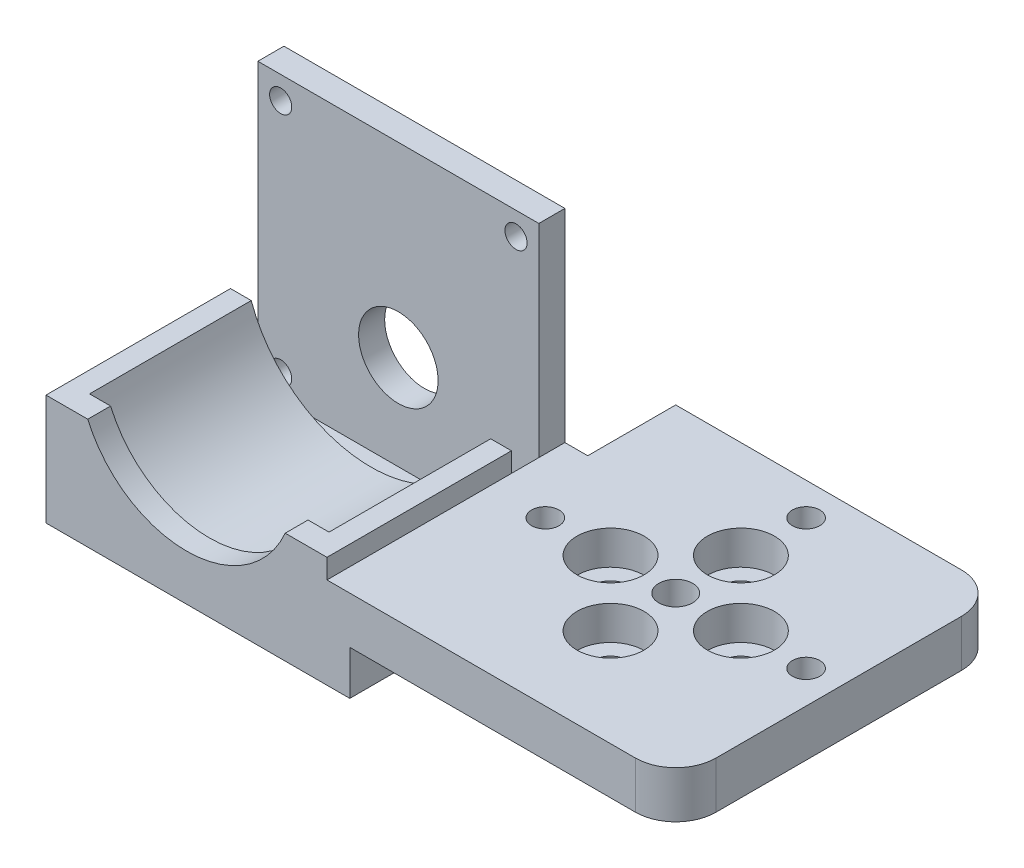
SolidWorks part; units mm, degrees
ref_plane "정면" through (0, 0, 0) normal (0, 0, 1) x (1, 0, 0)
ref_plane "윗면" through (0, 0, 0) normal (0, 1, 0) x (1, 0, 0)
ref_plane "우측면" through (0, 0, 0) normal (1, 0, 0) x (0, 0, -1)
sketch "스케치2" plane through (0, 0, 0) normal (0, 1, 0) x (1, 0, 0)
  line L1 (-25, 25) -> (25, 25)
  line L2 (-25, 25) -> (-25, -25)
  line L3 (-25, -25) -> (25, -25)
  line L4 (25, 25) -> (25, -25)
  line L5 (-25, 25) -> (25, -25) construction
  line L6 (-25, -25) -> (25, 25) construction
  circle A0 centre (0, 0) radius 2.6
  circle A1 centre (10, 0) radius 2.6
  circle A2 centre (0, -10) radius 2.6
  circle A3 centre (-10, 0) radius 2.6
  circle A4 centre (0, 10) radius 2.6
  point P4 (0, 0)
  point P19 (0, 0)
  dimension "D3" = 5.2
  dimension "D1" = 50
  dimension "D2" = 50
  dimension "D4" = 10
  dimension "D5" = 4
extrude "보스-돌출1" add sketch "스케치2" along normal blind 2
sketch "스케치3" plane through (0, 2, 0) normal (0, 1, 0) x (1, 0, 0)
  line L0 (25, -25) -> (25, 25) construction
  line L1 (-25, 25) -> (25, 25)
  line L2 (-25, 25) -> (-25, -25)
  line L3 (-25, -25) -> (25, -25)
  line L4 (25, 25) -> (25, -25)
  line L5 (-25, 25) -> (25, -25) construction
  line L6 (-25, -25) -> (25, 25) construction
  circle A0 centre (0, 0) radius 5.15 construction
  circle A1 centre (10, 0) radius 5.15
  circle A2 centre (10, 0) radius 2.6 construction
  circle A3 centre (0, -10) radius 5.15
  circle A4 centre (-10, 0) radius 5.15
  circle A5 centre (0, 10) radius 5.15
  circle A6 centre (-10, 0) radius 2.6 construction
  point P15 (0, 0)
  point P23 (0, 0)
  dimension "D1" = 10.3
  dimension "D2" = 4
extrude "보스-돌출2" add sketch "스케치3" along normal blind 5.2
sketch "스케치4" plane through (0, 7.2, 0) normal (0, 1, 0) x (1, 0, 0)
  line L0 (-25, -25) -> (25, -25) construction
  line L1 (-10, 10) -> (10, 10) construction
  line L2 (-10, 10) -> (-10, -25) construction
  line L3 (-10, -25) -> (10, -25) construction
  line L4 (10, 10) -> (10, -25) construction
  line L5 (-10, 10) -> (10, -25) construction
  line L6 (-10, -25) -> (10, 10) construction
  line L7 (0, 0) -> (20, 0) construction
  line L8 (0, 0) -> (0, 20) construction
  circle A2 centre (20, 0) radius 2.1
  circle A3 centre (0, 20) radius 2.1
  circle A4 centre (-20, 0) radius 2.1
  point P4 (0, -7.5)
  point P8 (0, -25)
  dimension "D4" = 4.2
  dimension "D1" = 20
  dimension "D2" = 10
  dimension "D3" = 20
  dimension "D6" = 90
  dimension "D5" = 3
extrude "컷-돌출1" cut sketch "스케치4" against normal blind 10
sketch "스케치6" plane through (0, 0, 0) normal (0, -1, 0) x (1, 0, 0)
  line L13 (-25, -25) -> (-25, 25) construction
  line L14 (-16.45, -2.0496) -> (-16.45, 2.0496)
  line L15 (-16.45, 2.0496) -> (-20, 4.0992)
  line L16 (-20, 4.0992) -> (-23.55, 2.0496)
  line L17 (-23.55, 2.0496) -> (-23.55, -2.0496)
  line L18 (-23.55, -2.0496) -> (-20, -4.0992)
  line L19 (-20, -4.0992) -> (-16.45, -2.0496)
  line L20 (2.0496, -16.45) -> (-2.0496, -16.45)
  line L21 (-2.0496, -16.45) -> (-4.0992, -20)
  line L22 (-4.0992, -20) -> (-2.0496, -23.55)
  line L23 (-2.0496, -23.55) -> (2.0496, -23.55)
  line L24 (2.0496, -23.55) -> (4.0992, -20)
  line L25 (4.0992, -20) -> (2.0496, -16.45)
  line L26 (16.45, 2.0496) -> (16.45, -2.0496)
  line L27 (16.45, -2.0496) -> (20, -4.0992)
  line L28 (20, -4.0992) -> (23.55, -2.0496)
  line L29 (23.55, -2.0496) -> (23.55, 2.0496)
  line L30 (23.55, 2.0496) -> (20, 4.0992)
  line L31 (20, 4.0992) -> (16.45, 2.0496)
  line L32 (0, 0) -> (-16.45, 2.0496) construction
  line L33 (0, 0) -> (-2.0496, -16.45) construction
  circle A0 centre (-20, 0) radius 3.55 construction
  circle A2 centre (0, -20) radius 3.55 construction
  circle A3 centre (20, 0) radius 3.55 construction
  dimension "D1" = 7.1
  dimension "D3" = 90
  dimension "D2" = 3
extrude "컷-돌출2" cut sketch "스케치6" against normal blind 3.5
fillet "필렛1" radius 6.17 1 edges at (25, 3.6, -25)
fillet "필렛2" radius 6.17 1 edges at (25, 3.6, 25)
ref_plane "평면1" through (0, 0, -11.5) normal (0, 0, -1) x (-1, 0, 0)
ref_plane "평면2" through (0, 9.71, 0) normal (0, -1, 0) x (-1, 0, 0)
sketch "스케치7" plane through (0, 0, -11.5) normal (0, 0, -1) x (-1, 0, 0)
  line L0 (-27.5, 9.71) -> (27.5, 9.71) construction
  line L1 (28.5, -4.79) -> (71.6, -4.79)
  line L2 (28.5, -4.79) -> (28.5, 38.31)
  line L3 (28.5, 38.31) -> (71.6, 38.31)
  line L4 (71.6, -4.79) -> (71.6, 38.31)
  line L5 (28.5, -4.79) -> (71.6, 38.31) construction
  line L6 (28.5, 38.31) -> (71.6, -4.79) construction
  line L7 (25, 7.2) -> (25, 0) construction
  circle A0 centre (50.05, 9.71) radius 6.1
  circle A1 centre (68.1, 34.81) radius 1.7
  circle A2 centre (68.1, -1.29) radius 1.7
  circle A3 centre (32, -1.29) radius 1.7
  circle A4 centre (32, 34.81) radius 1.7
  point P4 (50.05, 16.76)
  point P7 (0, 0)
  point P8 (0, 0)
  point P22 (50.05, 16.76)
  dimension "D3" = 12.2
  dimension "D4" = 14.5
  dimension "D6" = 3.4
  dimension "D1" = 43.1
  dimension "D2" = 43.1
  dimension "D5" = 3.5
  dimension "D7" = 3.5
  dimension "D8" = 4
extrude "보스-돌출3" add sketch "스케치7" against normal blind 4 separate body
sketch "스케치8" plane through (0, 0, -7.5) normal (0, 0, 1) x (1, 0, 0)
  line L0 (-71.6, -4.79) -> (-71.6, 38.31) construction
  line L1 (-71.6, 10.21) -> (-68.417, 10.21)
  line L2 (-71.6, 10.21) -> (-71.6, -4.79)
  line L3 (-71.6, -4.79) -> (-28.5, -4.79)
  line L4 (-28.5, 10.21) -> (-28.5, -4.79)
  line L5 (-71.6, 10.21) -> (-28.5, -4.79) construction
  line L6 (-71.6, -4.79) -> (-28.5, 10.21) construction
  line L7 (-28.5, -4.79) -> (-71.6, -4.79) construction
  line L9 (-28.5, 38.31) -> (-28.5, -4.79) construction
  line L10 (-31.683, 10.21) -> (-28.5, 10.21)
  arc A0 (-68.417, 10.21) -> (-31.683, 10.21) centre (-50.05, 16.76) ccw
  point P8 (-50.05, 2.71)
  dimension "D1" = 39
  dimension "D2" = 15
extrude "보스-돌출4" add sketch "스케치8" along normal blind 29
sketch "스케치9" plane through (0, 0, 21.5) normal (0, 0, 1) x (1, 0, 0)
  line L0 (-28.5, 38.31) -> (-71.6, -4.79) construction
  line L1 (-34.9058, 10.21) -> (-28.5, 10.21)
  line L2 (-71.6, 10.21) -> (-65.1942, 10.21)
  line L3 (-71.6, 10.21) -> (-71.6, -4.79)
  line L4 (-71.6, -4.79) -> (-28.5, -4.79)
  line L5 (-28.5, 10.21) -> (-28.5, -4.79)
  line L6 (-71.6, 10.21) -> (-28.5, -4.79) construction
  line L7 (-71.6, -4.79) -> (-28.5, 10.21) construction
  arc A0 (-65.1942, 10.21) -> (-34.9058, 10.21) centre (-50.05, 16.76) ccw
  point P8 (-50.05, 2.71)
  dimension "D1" = 33
extrude "보스-돌출5" add sketch "스케치9" along normal up to vertex (3.5 mm away)
sketch "스케치10" plane through (0, 0, 25) normal (0, 0, 1) x (1, 0, 0)
  line L1 (-28.5, -4.79) -> (-25, -4.79)
  line L2 (-28.5, -4.79) -> (-28.5, 7.2)
  line L3 (-28.5, 7.2) -> (-25, 7.2)
  line L4 (-25, -4.79) -> (-25, 7.2)
  line L5 (-28.5, -4.79) -> (-25, 7.2) construction
  line L6 (-28.5, 7.2) -> (-25, -4.79) construction
  point P4 (-26.75, 1.205)
extrude "보스-돌출6" add sketch "스케치10" against normal up to vertex (36.5 mm away) up to point (-28.5, -4.79, -11.5)
sketch "스케치11" plane through (0, 0, -7.5) normal (0, 0, 1) x (1, 0, 0)
  line L1 (-71.6, 38.31) -> (-28.5, 38.31)
  line L2 (-71.6, 38.31) -> (-71.6, -4.79)
  line L3 (-71.6, -4.79) -> (-28.5, -4.79)
  line L4 (-28.5, 38.31) -> (-28.5, -4.79)
  line L5 (-71.6, 38.31) -> (-28.5, -4.79) construction
  line L6 (-71.6, -4.79) -> (-28.5, 38.31) construction
  point P4 (-50.05, 16.76)
extrude "컷-돌출3" cut sketch "스케치11" along normal blind 4.2
sketch "스케치12" plane through (0, -4.79, 0) normal (0, -1, 0) x (1, 0, 0)
  line L0 (-3.96, -11.5) -> (3.96, -11.5) construction
  line L1 (-71.6, 25) -> (-25, 25)
  line L2 (-71.6, 25) -> (-71.6, -11.5)
  line L3 (-71.6, -11.5) -> (-25, -11.5)
  line L4 (-25, 25) -> (-25, -11.5)
  line L5 (-71.6, 25) -> (-25, -11.5) construction
  line L6 (-71.6, -11.5) -> (-25, 25) construction
  line L7 (-25, -11.5) -> (-25, 25) construction
  point P4 (-48.3, 6.75)
extrude "보스-돌출7" add sketch "스케치12" along normal blind 2
sketch "스케치13" plane through (0, 0, -11.5) normal (0, 0, -1) x (-1, 0, 0)
  circle A0 centre (68.1, 34.81) radius 1.7
  circle A1 centre (68.1, -1.29) radius 1.7
  circle A2 centre (32, -1.29) radius 1.7
  circle A3 centre (32, 34.81) radius 1.7
  point P12 (50.05, 16.76)
  dimension "D1" = 3.4
  dimension "D2" = 4
extrude "컷-돌출4" cut sketch "스케치13" against normal blind 12
